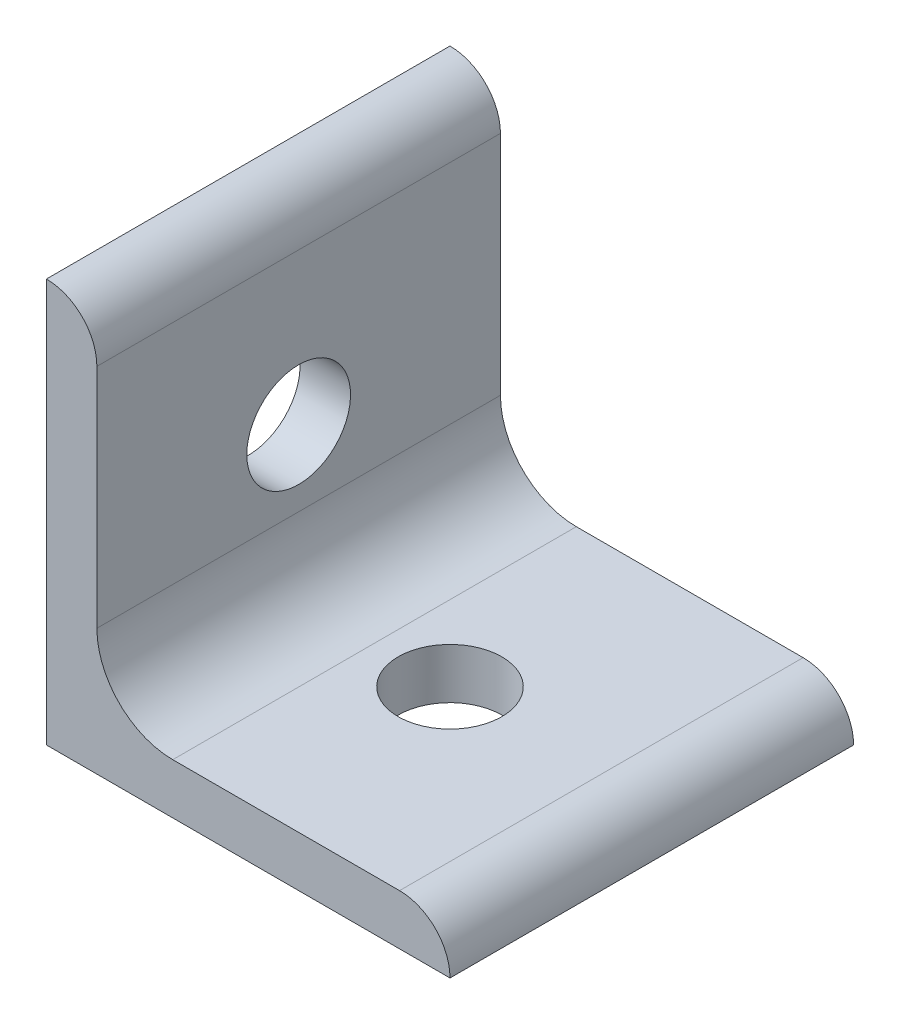
SolidWorks part; units mm, degrees
ref_plane "Front Plane" through (0, 0, 0) normal (0, 0, 1) x (1, 0, 0)
ref_plane "Top Plane" through (0, 0, 0) normal (0, 1, 0) x (1, 0, 0)
ref_plane "Right Plane" through (0, 0, 0) normal (1, 0, 0) x (0, 0, -1)
ref_plane "Plane1" through (0, 0, 25.4) normal (0, 0, 1) x (1, 0, 0)
sketch "Sketch1" plane through (0, 0, 25.4) normal (0, 0, 1) x (1, 0, 0)
  line L0 (23.473, -1.6964) -> (23.473, -27.0964)
  line L1 (23.473, -27.0964) -> (48.873, -27.0964)
  line L2 (45.698, -23.9214) -> (26.648, -23.9214)
  line L3 (26.648, -23.9214) -> (26.648, -4.8714)
  arc A0 (48.873, -27.0964) -> (45.698, -23.9214) centre (45.698, -27.0964) ccw
  arc A1 (26.648, -4.8714) -> (23.473, -1.6964) centre (23.473, -4.8714) ccw
extrude "Boss-Extrude1" add sketch "Sketch1" against normal blind 25.4
hole_wizard "M6 Clearance Hole1" positions "Sketch3" profile "Sketch2" hole size "M6" standard "Ansi Metric"
sketch "Sketch3" plane through (0, -27.0964, 0) normal (0, -1, 0) x (1, 0, 0)
  point P0 (36.173, 12.7)
sketch "Sketch2" plane through (36.173, -27.0964, 12.7) normal (1, 0, 0) x (0, 0, -1)
  line L0 (0, 0) -> (0, 25.4)
  line L1 (0, 25.4) -> (3.2639, 25.4)
  line L2 (3.2639, 25.4) -> (3.2639, 0)
  line L5 (3.2639, 0) -> (0, 0)
  line L11 (0, -6.35) -> (0, 107.95) construction
  dimension "Thru Hole Dia." = 6.5278
  dimension "Thru Hole Depth" = 25.4
hole_wizard "M6 Clearance Hole2" positions "Sketch5" profile "Sketch4" hole size "M6" standard "Ansi Metric"
sketch "Sketch5" plane through (23.473, 0, 0) normal (-1, 0, 0) x (0, 0, 1)
  point P0 (12.7, -14.3964)
sketch "Sketch4" plane through (23.473, -14.3964, 12.7) normal (0, 1, 0) x (0, 0, 1)
  line L0 (0, 0) -> (0, 25.4)
  line L1 (0, 25.4) -> (3.2639, 25.4)
  line L2 (3.2639, 25.4) -> (3.2639, 0)
  line L5 (3.2639, 0) -> (0, 0)
  line L11 (0, -6.35) -> (0, 107.95) construction
  dimension "Thru Hole Dia." = 6.5278
  dimension "Thru Hole Depth" = 25.4
fillet "Fillet1" radius 4.7752 1 edges at (26.648, -23.9214, 12.7)
